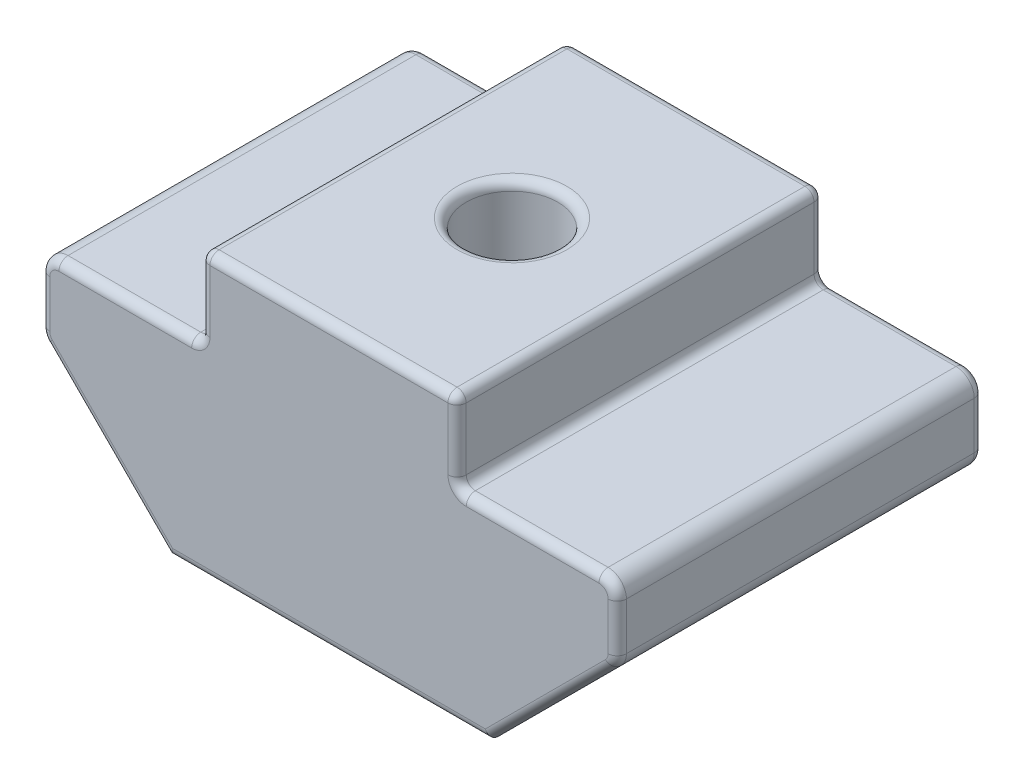
SolidWorks part; units mm, degrees
material "1060 Alloy"
ref_plane "Front Plane" through (0, 0, 0) normal (0, 0, 1) x (1, 0, 0)
ref_plane "Top Plane" through (0, 0, 0) normal (0, 1, 0) x (1, 0, 0)
ref_plane "Right Plane" through (0, 0, 0) normal (1, 0, 0) x (0, 0, -1)
sketch "Sketch1" plane through (0, 0, 0) normal (0, 0, 1) x (1, 0, 0)
  line L0 (-4.375, 0) -> (4.375, 0)
  line L1 (4.375, 0) -> (7.875, 3.5)
  line L3 (-7.875, 3.5) -> (-4.375, 0)
  line L4 (-7.875, 3.5) -> (-7.875, 5.5)
  line L6 (7.875, 5.5) -> (7.875, 3.5)
  line L7 (-7.875, 5.5) -> (-3.5, 5.5)
  line L8 (-3.5, 5.5) -> (-3.5, 7.7)
  line L9 (-3.5, 7.7) -> (3.5, 7.7)
  line L10 (3.5, 7.7) -> (3.5, 5.5)
  line L11 (3.5, 5.5) -> (7.875, 5.5)
  point P4 (0, 0)
  point P14 (0, 7.7)
  dimension "D1" = 45
  dimension "D2" = 15.75
  dimension "D3" = 5.5
  dimension "D4" = 2
  dimension "D5" = 2.2
  dimension "D6" = 7
extrude "Boss-Extrude1" add sketch "Sketch1" along normal mid plane 10
sketch "Sketch2" plane through (0, 7.7, 0) normal (0, 1, 0) x (1, 0, 0)
  circle A0 centre (0, 0) radius 1.25
  dimension "D1" = 2.5
extrude "Cut-Extrude1" cut sketch "Sketch2" against normal through all
fillet "Fillet1" radius 0.5 4 edges at (7.875, 3.5, 0) (7.875, 5.5, 0) (-7.875, 3.5, 0) (-7.875, 5.5, 0)
fillet "Fillet2" radius 0.25 33 edges at (7.7286, 5.3536, -5) (5.4375, 5.5, -5) (3.5, 6.6, -5) (0, 7.7, -5) (-3.5, 6.6, -5) (-5.4375, 5.5, -5) (-7.7286, 5.3536, -5) (-7.875, 4.3536, -5) (-7.8369, 3.5158, -5) (-6.0518, 1.6768, -5) (0, 0, -5) (6.0518, 1.6768, -5) (7.8369, 3.5158, -5) (7.875, 4.3536, -5) (0, 0, 5) (-6.0518, 1.6768, 5) (-7.8369, 3.5158, 5) (-7.875, 4.3536, 5) (-7.7286, 5.3536, 5) (-5.4375, 5.5, 5) (-3.5, 6.6, 5) (0, 7.7, 5) (3.5, 6.6, 5) (5.4375, 5.5, 5) (7.7286, 5.3536, 5) (7.875, 4.3536, 5) (7.8369, 3.5158, 5) (6.0518, 1.6768, 5) (3.5, 7.7, 0) (-3.5, 7.7, 0) (-1.25, 7.7, 0) (3.5, 5.5, 0) (-3.5, 5.5, 0)
